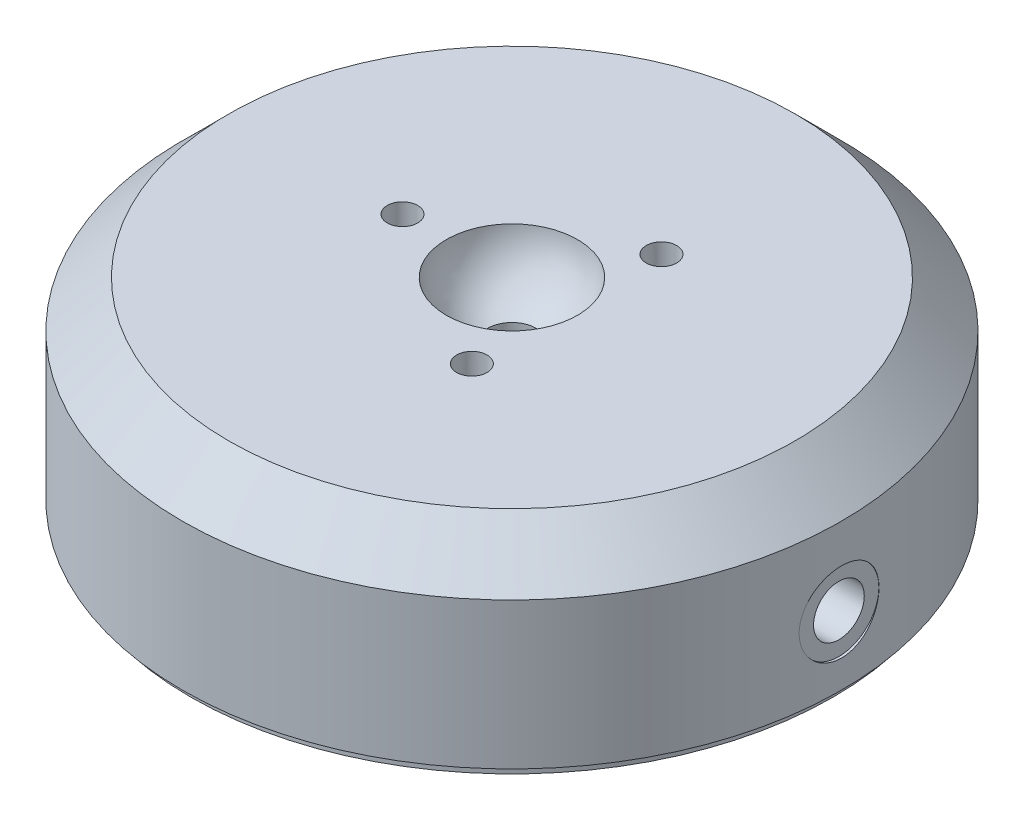
SolidWorks part; units mm, degrees
material "6061 Alloy"
ref_plane "Front Plane" through (0, 0, 0) normal (0, 0, 1) x (1, 0, 0)
ref_plane "Top Plane" through (0, 0, 0) normal (0, 1, 0) x (1, 0, 0)
ref_plane "Right Plane" through (0, 0, 0) normal (1, 0, 0) x (0, 0, -1)
sketch "Sketch1" plane through (0, 0, 0) normal (0, 1, 0) x (1, 0, 0)
  circle A0 centre (0, 0) radius 32.5
  dimension "D1" = 65
extrude "Extrude1" add sketch "Sketch1" along normal blind 18.9992
sketch "Sketch2" plane through (0, 0, 0) normal (0, -1, 0) x (1, 0, 0)
  circle A0 centre (0, 0) radius 31.6865
  dimension "D1" = 63.373
sketch "Sketch3" plane through (0, 0, 0) normal (0, 0, 1) x (1, 0, 0)
  line L0 (0, 18.9992) -> (0, 0) construction
  line L1 (32.5, 18.9992) -> (-32.5, 18.9992) construction
  line L2 (2.3876, 13.4638) -> (2.3876, 12.7508)
  line L3 (2.3876, 12.7508) -> (0, 12.7508)
  line L4 (0, 12.7508) -> (2.3876, 12.7508)
  line L5 (32.5, 0) -> (32.5, 18.9992) construction
  line L6 (0, 12.7508) -> (0, 18.9992)
  line L7 (0, 18.9992) -> (6.4705, 18.9992)
  arc A0 (2.3876, 13.4638) -> (6.4705, 18.9992) centre (-0.012, 19.5072) ccw
  dimension "D1" = 6.5024
  dimension "D2" = 0.508
  dimension "D3" = 2.3876
  dimension "D4" = 6.2484
  dimension "D5" = 32.512
revolve "Cut-Revolve1" cut sketch "Sketch3" angle 360 about L0
chamfer "Chamfer1" distance 4.57 angle 45 1 edges at (0, 18.9992, 32.5)
sketch "Sketch4" plane through (0, 18.9992, 0) normal (0, 1, 0) x (-1, 0, 0)
  line L0 (0, 0) -> (10.795, 0) construction
  line L1 (0, 0) -> (-5.3975, -9.3487) construction
  line L3 (0, 0) -> (-5.3975, 9.3487) construction
  circle A0 centre (0, 0) radius 10.795 construction
  dimension "D1" = 21.59
  dimension "D2" = 120
  dimension "D3" = 120
hole_wizard "M3x0.5 Tapped Hole3" positions "Sketch10" profile "Sketch9" tap size "M3x0.5" standard "Ansi Metric"
sketch "Sketch10" plane through (0, 18.9992, 0) normal (0, 1, 0) x (-1, 0, 0)
  point P0 (-5.3975, -9.3487)
  point P1 (10.795, 0)
  point P4 (-5.3975, 9.3487)
sketch "Sketch9" plane through (5.3975, 18.9992, -9.3487) normal (1, 0, 0) x (0, 0, 1)
  line L0 (0, 0) -> (0, 8.5997)
  line L1 (0, 8.5997) -> (1.25, 7.8486)
  line L2 (1.25, 7.8486) -> (1.25, 6.35)
  line L3 (1.25, 6.35) -> (1.5, 6.35)
  line L4 (1.5, 6.35) -> (1.5, 0)
  line L5 (1.5, 0) -> (0, 0)
  line L10 (0, 8.5997) -> (-1.25, 7.8486) construction
  line L11 (0, -6.35) -> (0, 107.95) construction
  dimension "Tap Drill Dia." = 2.5
  dimension "Tap Drill Depth" = 7.8486
  dimension "Thread Major Dia." = 3
  dimension "Thread Depth" = 6.35
  dimension "Drill Angle" = 118
hole_wizard "M5x0.8 Tapped Hole1" positions "3DSketch1" profile "Sketch11" tap size "M5x0.8" standard "Ansi Metric"
sketch3d "3DSketch1"
  point P0 (32.5, 6.6802, 0)
  point P1 (0, 0, 0)
  dimension "D1" = 12.319
sketch "Sketch11" plane through (32.5, 6.6802, 0) normal (0, 1, 0) x (0, 0, -1)
  line L0 (0, 0) -> (0, 29.2018)
  line L1 (0, 29.2018) -> (2.1, 27.94)
  line L2 (2.1, 27.94) -> (2.1, 7.62)
  line L3 (2.1, 7.62) -> (2.5, 7.62)
  line L4 (2.5, 7.62) -> (2.5, 0)
  line L5 (2.5, 0) -> (0, 0)
  line L10 (0, 29.2018) -> (-2.1, 27.94) construction
  line L11 (0, -6.35) -> (0, 107.95) construction
  dimension "Tap Drill Dia." = 4.2
  dimension "Tap Drill Depth" = 27.94
  dimension "Thread Major Dia." = 5
  dimension "Thread Depth" = 7.62
  dimension "Drill Angle" = 118
hole_wizard "Hole1" positions "3DSketch2" profile "Sketch13" legacy
sketch3d "3DSketch2"
  line L3 (24.88, 6.6802, 0) -> (32.4037, 6.6802, 0) construction
  point P0 (32.5, 6.6802, 0)
sketch "Sketch13" plane through (32.5, 6.6802, 0) normal (0, 1, 0) x (0, 0, -1)
  line L0 (0, 0) -> (0, 7.2657)
  line L1 (0, 7.2657) -> (1.524, 6.35)
  line L2 (1.524, 6.35) -> (1.524, 0.254)
  line L3 (1.524, 0.254) -> (3.937, 0.254)
  line L4 (3.937, 0) -> (0, 0)
  line L5 (0, -11.3109) -> (0, 121.1557) construction
  line L6 (0, 7.2657) -> (-1.524, 6.35) construction
  line L7 (3.937, 0.254) -> (3.937, 0)
  dimension "Depth" = 6.35
  dimension "Drill Angle" = 118
  dimension "Diameter" = 3.048
  dimension "C-Bore Diameter" = 7.874
  dimension "C-Bore Depth" = 0.254
extrude "Extrude2" add sketch "Sketch2" along normal blind 1.0008
